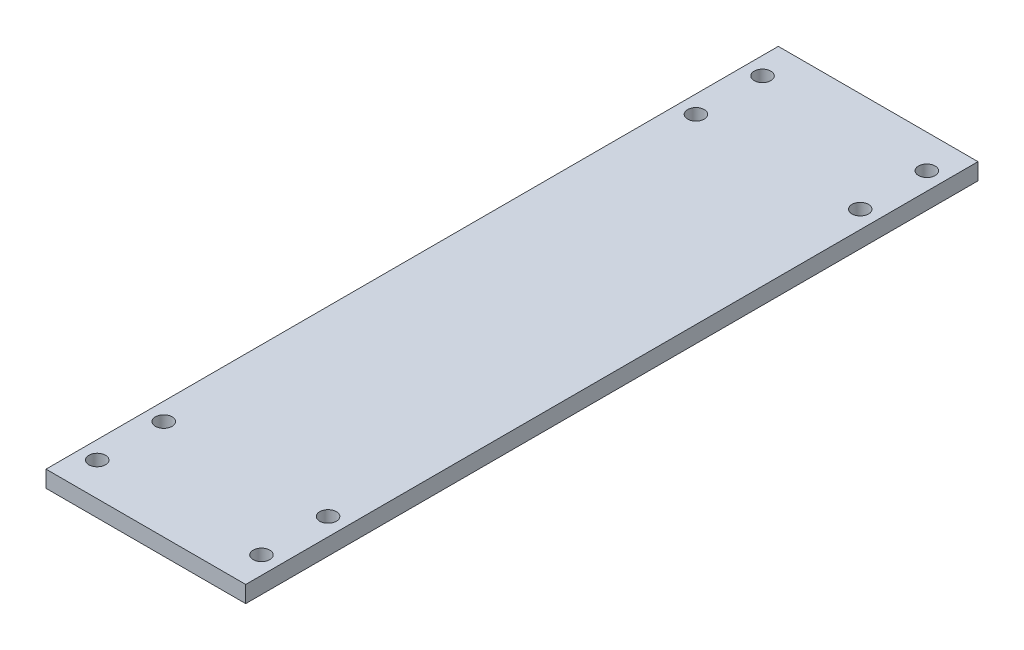
SolidWorks part; units mm, degrees
ref_plane "Front Plane" through (0, 0, 0) normal (0, 0, 1) x (1, 0, 0)
ref_plane "Top Plane" through (0, 0, 0) normal (0, 1, 0) x (1, 0, 0)
ref_plane "Right Plane" through (0, 0, 0) normal (1, 0, 0) x (0, 0, -1)
sketch "Sketch1" plane through (0, 0, 0) normal (0, 1, 0) x (1, 0, 0)
  line L1 (-152.4, 0) -> (0, 0)
  line L2 (-152.4, 0) -> (-152.4, -558.8)
  line L3 (-152.4, -558.8) -> (0, -558.8)
  line L4 (0, 0) -> (0, -558.8)
  dimension "D1" = 558.8
  dimension "D2" = 152.4
extrude "Boss-Extrude1" add sketch "Sketch1" along normal blind 12.7
sketch "Sketch2" plane through (0, 0, 0) normal (0, -1, 0) x (-1, 0, 0)
  line L0 (76.2, 0) -> (76.2, -558.8) construction
  line L1 (0, 0) -> (152.4, 0) construction
  line L2 (152.4, -558.8) -> (0, -558.8) construction
  line L3 (0, -279.4) -> (152.4, -279.4) construction
  line L4 (0, -558.8) -> (0, 0) construction
  line L5 (152.4, 0) -> (152.4, -558.8) construction
  circle A0 centre (13.5143, -25.5474) radius 6.35
  circle A1 centre (13.5143, -76.3474) radius 6.35
  circle A2 centre (13.5143, -482.4526) radius 6.35
  circle A3 centre (13.5143, -533.2526) radius 6.35
  circle A4 centre (138.8857, -76.3474) radius 6.35
  circle A5 centre (138.8857, -25.5474) radius 6.35
  circle A6 centre (138.8857, -482.4526) radius 6.35
  circle A7 centre (138.8857, -533.2526) radius 6.35
  dimension "D1" = 12.7
extrude "Cut-Extrude1" cut sketch "Sketch2" against normal up to next
